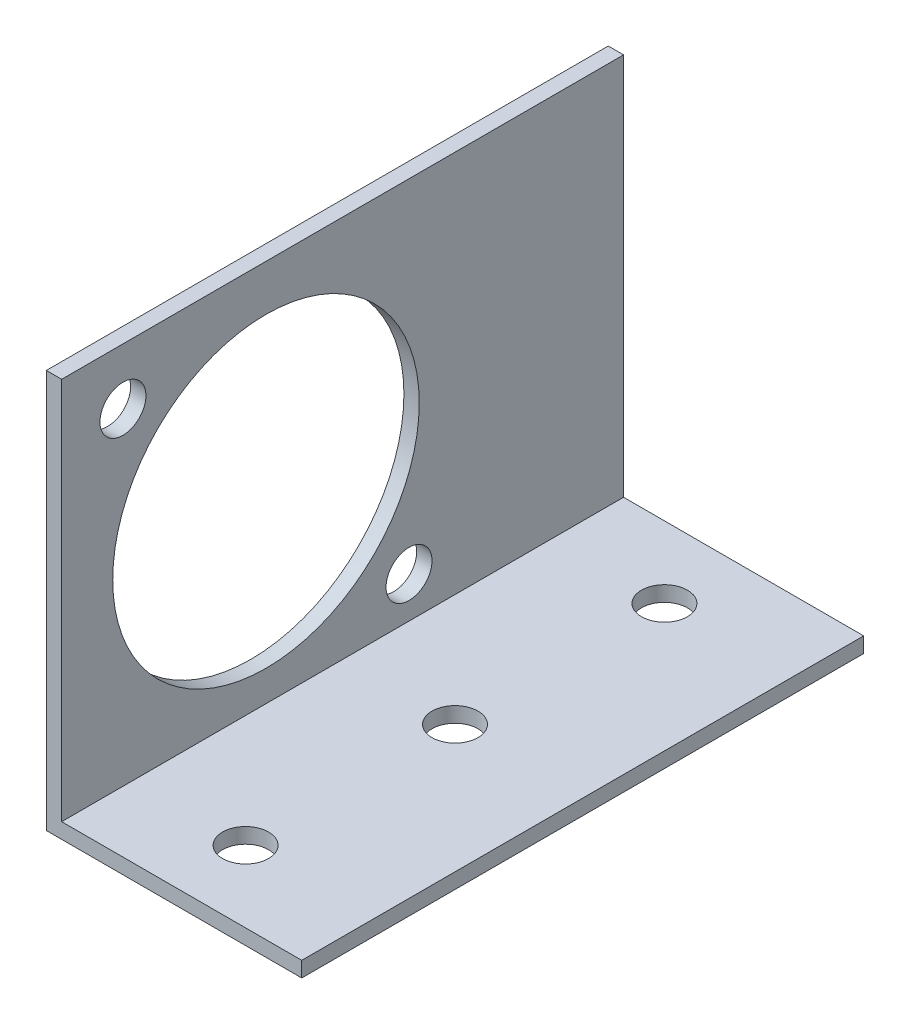
SolidWorks part; units mm, degrees
ref_plane "Plan de face" through (0, 0, 0) normal (0, 0, 1) x (1, 0, 0)
ref_plane "Plan de dessus" through (0, 0, 0) normal (0, 1, 0) x (1, 0, 0)
ref_plane "Plan de droite" through (0, 0, 0) normal (1, 0, 0) x (0, 0, -1)
sketch "Esquisse1" plane through (0, 0, 0) normal (0, 0, 1) x (1, 0, 0)
  line L0 (0, 0) -> (25, 0)
  line L1 (0, 0) -> (0, 39)
  dimension "D1" = 39
  dimension "D2" = 25
extrude "Extru.-Mince1" add sketch "Esquisse1" against normal blind 55 thin thin type one direction wall 1.5
sketch "Esquisse2" plane through (0, 1.5, 0) normal (0, 1, 0) x (-1, 0, 0)
  line L0 (-25, 0) -> (-1.5, 0) construction
  line L1 (-25, -55) -> (-1.5, -55) construction
  line L2 (-25, -55) -> (-25, 0) construction
  point P0 (-12.5, -7)
  point P1 (-12.5, -27.5)
  point P2 (-12.5, -48)
  dimension "D1" = 7
  dimension "D2" = 7
  dimension "D3" = 27.5
  dimension "D4" = 12.5
  dimension "D5" = 12.5
  dimension "D6" = 12.5
hole_wizard "Dégagement M41" positions "Esquisse8" profile "Esquisse9" hole size "M4" standard "ISO" end condition through all
sketch "Esquisse8" plane through (0, 1.5, 0) normal (0, 1, 0) x (-1, 0, 0)
  point P1 (-12.5, -7)
  point P4 (-12.5, -27.5)
  point P7 (-12.5, -48)
sketch "Esquisse9" plane through (12.5, 1.5, -7) normal (1, 0, 0) x (0, 0, 1)
  line L0 (0, 0) -> (0, 1.5)
  line L1 (0, 1.5) -> (2.25, 1.5)
  line L2 (2.25, 1.5) -> (2.25, 0)
  line L5 (2.25, 0) -> (0, 0)
  line L11 (0, -6.35) -> (0, 107.95) construction
  dimension "Diamètre du perçage jusqu'au prochain" = 4.5
  dimension "Profondeur du perçage jusqu'au prochain" = 1.5
sketch "Esquisse10" plane through (1.5, 0, 0) normal (1, 0, 0) x (0, 0, -1)
  line L0 (55, 39) -> (0, 39) construction
  line L1 (0, 1.5) -> (0, 39) construction
  line L2 (6, 33.5) -> (34, 5.5) construction
  point P0 (20, 19.5)
  point P5 (34, 5.5)
  point P6 (6, 33.5)
  dimension "D1" = 19.5
  dimension "D2" = 20
  dimension "D3" = 6
  dimension "D4" = 5.5
  dimension "D5" = 33.5
  dimension "D6" = 34
hole_wizard "Dégagement M42" positions "Esquisse12" profile "Esquisse11" hole size "M4" standard "ISO" end condition through all
sketch "Esquisse12" plane through (1.5, 0, 0) normal (1, 0, 0) x (0, 0, -1)
  point P1 (6, 33.5)
  point P4 (34, 5.5)
sketch "Esquisse11" plane through (1.5, 33.5, -6) normal (0, 1, 0) x (0, 0, -1)
  line L0 (0, 0) -> (0, 1.5)
  line L1 (0, 1.5) -> (2.25, 1.5)
  line L2 (2.25, 1.5) -> (2.25, 0)
  line L5 (2.25, 0) -> (0, 0)
  line L11 (0, -6.35) -> (0, 107.95) construction
  dimension "Diamètre du perçage jusqu'au prochain" = 4.5
  dimension "Profondeur du perçage jusqu'au prochain" = 1.5
hole_wizard "Dégagement M271" positions "Esquisse14" profile "Esquisse13" hole size "M27" standard "ISO"
sketch "Esquisse14" plane through (1.5, 0, 0) normal (1, 0, 0) x (0, 0, -1)
  point P1 (20, 19.5)
sketch "Esquisse13" plane through (1.5, 19.5, -20) normal (0, 1, 0) x (0, 0, -1)
  line L0 (0, 0) -> (0, 10.5129)
  line L1 (0, 10.5129) -> (15, 1.5)
  line L2 (15, 1.5) -> (15, 0)
  line L5 (15, 0) -> (0, 0)
  line L10 (0, 10.5129) -> (-15, 1.5) construction
  line L11 (0, -6.35) -> (0, 107.95) construction
  dimension "Diamètre du perçage" = 30
  dimension "Profondeur du perçage" = 1.5
  dimension "Angle de pointe" = 118
